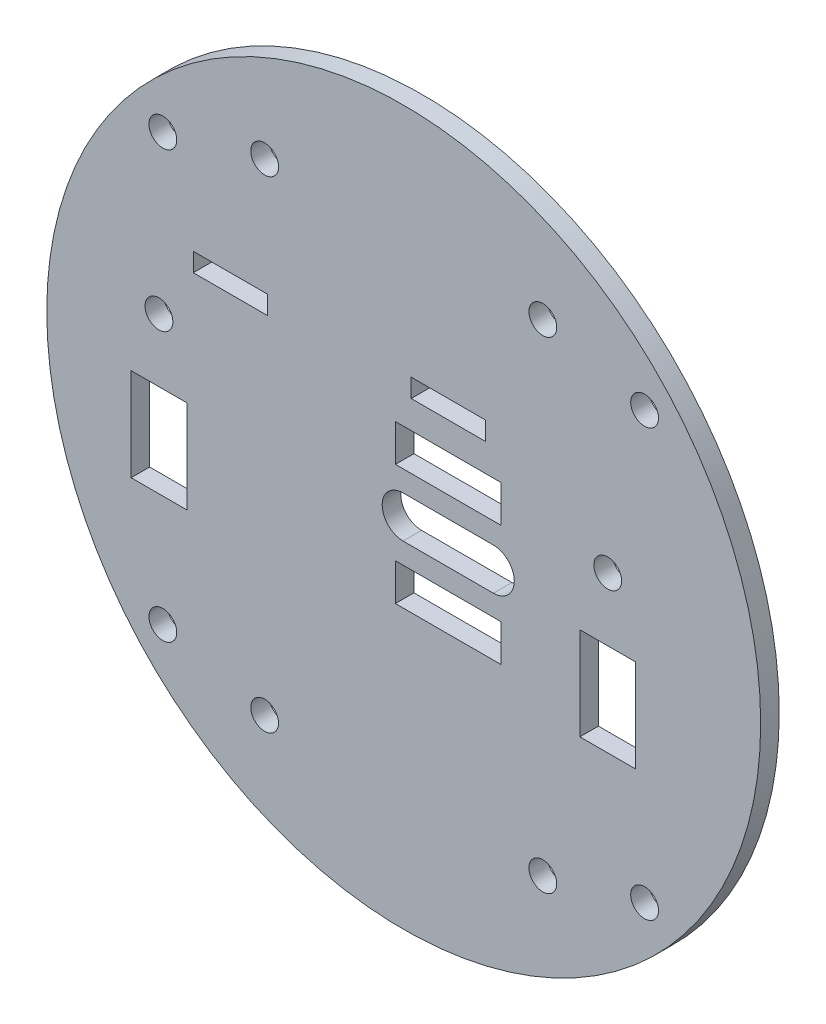
SolidWorks part; units mm, degrees
material "Acrylic (Medium-high impact)"
ref_plane "Front Plane" through (0, 0, 0) normal (0, 0, 1) x (1, 0, 0)
ref_plane "Top Plane" through (0, 0, 0) normal (0, 1, 0) x (1, 0, 0)
ref_plane "Right Plane" through (0, 0, 0) normal (1, 0, 0) x (0, 0, -1)
sketch "Model" plane through (0, 0, 0) normal (0, 0, 1) x (1, 0, 0)
  line L0 (-22.6266, 13.5) -> (-22.6266, 11.5)
  line L1 (-22.6266, 11.5) -> (-14.6266, 11.5)
  line L2 (-14.6266, 11.5) -> (-14.6266, 13.5)
  line L3 (-14.6266, 13.5) -> (-22.6266, 13.5)
  line L4 (0.8734, 13.5) -> (0.8734, 11.5)
  line L5 (0.8734, 13.5) -> (8.8734, 13.5)
  line L6 (8.8734, 13.5) -> (8.8734, 11.5)
  line L7 (8.8734, 11.5) -> (0.8734, 11.5)
  line L475 (-0.8266, -4.5) -> (10.5734, -4.5)
  line L476 (-0.8266, 4.5) -> (10.5734, 4.5)
  line L477 (0, -2.25) -> (9.7468, -2.25)
  line L478 (0, 2.25) -> (9.7468, 2.25)
  line L479 (-0.8266, 4.5) -> (-0.8266, 8.5)
  line L480 (10.5734, 4.5) -> (10.5734, 8.5)
  line L481 (10.5734, 8.5) -> (-0.8266, 8.5)
  line L482 (-0.8266, -4.5) -> (-0.8266, -8.5)
  line L483 (-0.8266, -8.5) -> (10.5734, -8.5)
  line L484 (10.5734, -8.5) -> (10.5734, -4.5)
  line L485 (-29.3266, -11) -> (-23.3266, -11)
  line L486 (-29.3266, -1) -> (-23.3266, -1)
  line L487 (19.0734, -1) -> (25.0734, -1)
  line L488 (19.0734, -11) -> (25.0734, -11)
  line L489 (-23.3266, -11) -> (-23.3266, -1)
  line L490 (-29.3266, -1) -> (-29.3266, -11)
  line L491 (19.0734, -1) -> (19.0734, -11)
  line L492 (25.0734, -1) -> (25.0734, -11)
  circle A171 centre (0.0734, 0) radius 38.5
  circle A172 centre (-14.9266, -25.9808) radius 1.5
  circle A173 centre (-14.9266, 25.9808) radius 1.5
  circle A174 centre (15.0734, 25.9808) radius 1.5
  circle A175 centre (15.0734, -25.9808) radius 1.5
  circle A176 centre (-26.3266, 5.806) radius 1.5
  circle A177 centre (22.0734, 5.806) radius 1.5
  circle A178 centre (26.0542, -23) radius 1.5
  circle A179 centre (-25.9074, -23) radius 1.5
  circle A180 centre (26.0542, 23) radius 1.5
  circle A181 centre (-25.9074, 23) radius 1.5
  arc A182 (9.7468, -2.25) -> (9.7468, 2.25) centre (9.7468, 0) ccw
  arc A183 (0, 2.25) -> (0, -2.25) centre (0, 0) ccw
  dimension "D1" = 3
  dimension "D2" = 77
  dimension "D3" = 2.25
  dimension "D4" = 0.0734
  dimension "D5" = 9.7468
  dimension "D6" = 10.5734
  dimension "D7" = 15.0734
  dimension "D8" = 19.0734
  dimension "D9" = 22.0734
  dimension "D10" = 25.0734
  dimension "D11" = 26.0542
  dimension "D12" = 0.8266
  dimension "D13" = 14.9266
  dimension "D14" = 23.3266
  dimension "D15" = 25.9074
  dimension "D16" = 26.3266
  dimension "D17" = 4.5
  dimension "D18" = 5.806
  dimension "D19" = 8.5
  dimension "D20" = 23
  dimension "D21" = 25.9808
  dimension "D22" = 1
  dimension "D23" = 4.5
  dimension "D24" = 9.5
  dimension "D25" = 11
  dimension "D26" = 23
  dimension "D27" = 25.9808
  dimension "D28" = 2
  dimension "D29" = 8
  dimension "D30" = 15.5
  dimension "D31" = 1.7
extrude "Boss-Extrude1" add sketch "Model" along normal blind 2
